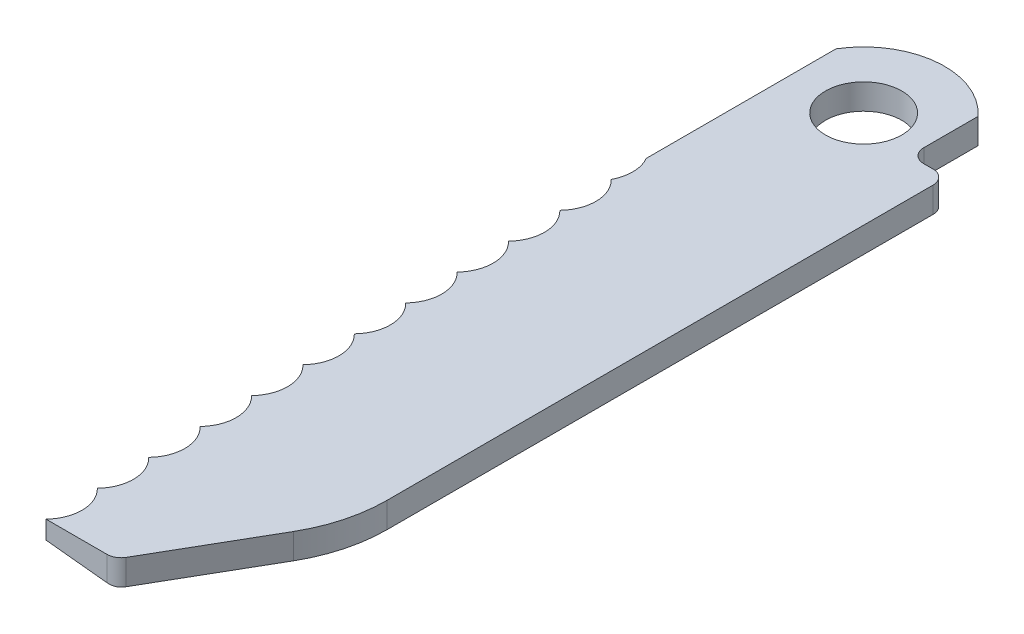
SolidWorks part; units mm, degrees
material "Plain Carbon Steel"
ref_plane "Front Plane" through (0, 0, 0) normal (0, 0, 1) x (1, 0, 0)
ref_plane "Top Plane" through (0, 0, 0) normal (0, 1, 0) x (1, 0, 0)
ref_plane "Right Plane" through (0, 0, 0) normal (1, 0, 0) x (0, 0, -1)
sketch "Sketch1" plane through (0, 0, 0) normal (0, 1, 0) x (1, 0, 0)
  line L0 (16.7853, 37.7669) -> (83.9265, 37.7669) construction
  line L1 (58.2518, 62.4076) -> (58.2518, 58.6683)
  line L2 (60.2838, 27.9343) -> (60.2838, 58.6683)
  line L3 (58.2518, 58.6683) -> (60.2838, 58.6683)
  line L4 (59.1949, 23.8703) -> (55.6134, 17.6669)
  line L5 (51.8151, 17.6669) -> (55.6134, 17.6669)
  line L6 (51.1398, 61.7219) -> (51.1398, 51.3023)
  line L7 (51.1398, 51.3023) -> (51.8151, 17.6669) construction
  arc A0 (51.1398, 61.7219) -> (58.2518, 62.4076) centre (54.9498, 59.4303) cw
  arc A3 (60.2838, 27.9343) -> (59.1949, 23.8703) centre (52.1558, 27.9343) cw
  arc A4 (51.1398, 51.3023) -> (51.1792, 49.342) centre (49.3735, 50.2863) cw
  arc A5 (51.7573, 20.5465) -> (51.8151, 17.6669) centre (50.3448, 19.0777) cw
  arc A6 (51.7573, 20.5465) -> (51.6995, 23.426) centre (50.287, 21.9573) ccw
  arc A7 (51.6417, 26.3056) -> (51.6995, 23.426) centre (50.2292, 24.8369) cw
  arc A8 (51.6417, 26.3056) -> (51.5839, 29.1851) centre (50.1714, 27.7164) ccw
  arc A9 (51.5261, 32.0647) -> (51.5839, 29.1851) centre (50.1136, 30.596) cw
  arc A10 (51.5261, 32.0647) -> (51.4682, 34.9442) centre (50.0558, 33.4755) ccw
  arc A11 (51.4104, 37.8238) -> (51.4682, 34.9442) centre (49.9979, 36.3551) cw
  arc A12 (51.3526, 40.7033) -> (51.4104, 37.8238) centre (49.9401, 39.2346) cw
  arc A13 (51.3526, 40.7033) -> (51.2948, 43.5829) centre (49.8823, 42.1142) ccw
  arc A14 (51.1792, 49.342) -> (51.237, 46.4624) centre (49.7667, 47.8733) cw
  arc A15 (51.237, 46.4624) -> (51.2948, 43.5829) centre (49.8245, 44.9937) cw
  circle A16 centre (54.9498, 59.4303) radius 2.0955
  dimension "D3" = 4.4461
  dimension "D7" = 5.334
  dimension "D8" = 0.762
  dimension "D9" = 31.496
  dimension "D10" = 2.794
  dimension "D11" = 8.128
  dimension "D12" = 2.0377
  dimension "D13" = 41.7634
  dimension "D14" = 9.144
  dimension "D15" = 11.557
  dimension "D16" = 35.56
  dimension "D2" = 4.191
  dimension "D4" = 8.128
  dimension "D5" = 3.302
  dimension "D6" = 3.81
extrude "Boss-Extrude1" add sketch "Sketch1" along normal blind 1.397
sketch "Sketch2" plane through (0, 0, 0) normal (0, 0, 1) x (1, 0, 0)
  line L0 (55.6134, 0) -> (51.1398, 0.4702)
  line L2 (51.1398, 0.4702) -> (51.1398, 0)
  line L3 (51.1398, 0) -> (55.6134, 0)
  line L4 (51.1398, 1.397) -> (51.1398, 0) construction
  dimension "D1" = 6
extrude "Cut-Extrude1" cut sketch "Sketch2" against normal blind 52.451
fillet "Fillet1" radius 0.762 3 edges at (60.2838, 0.6985, -58.6683) (58.2518, 0.6985, -58.6683) (55.6134, 0.6985, -17.6669)
